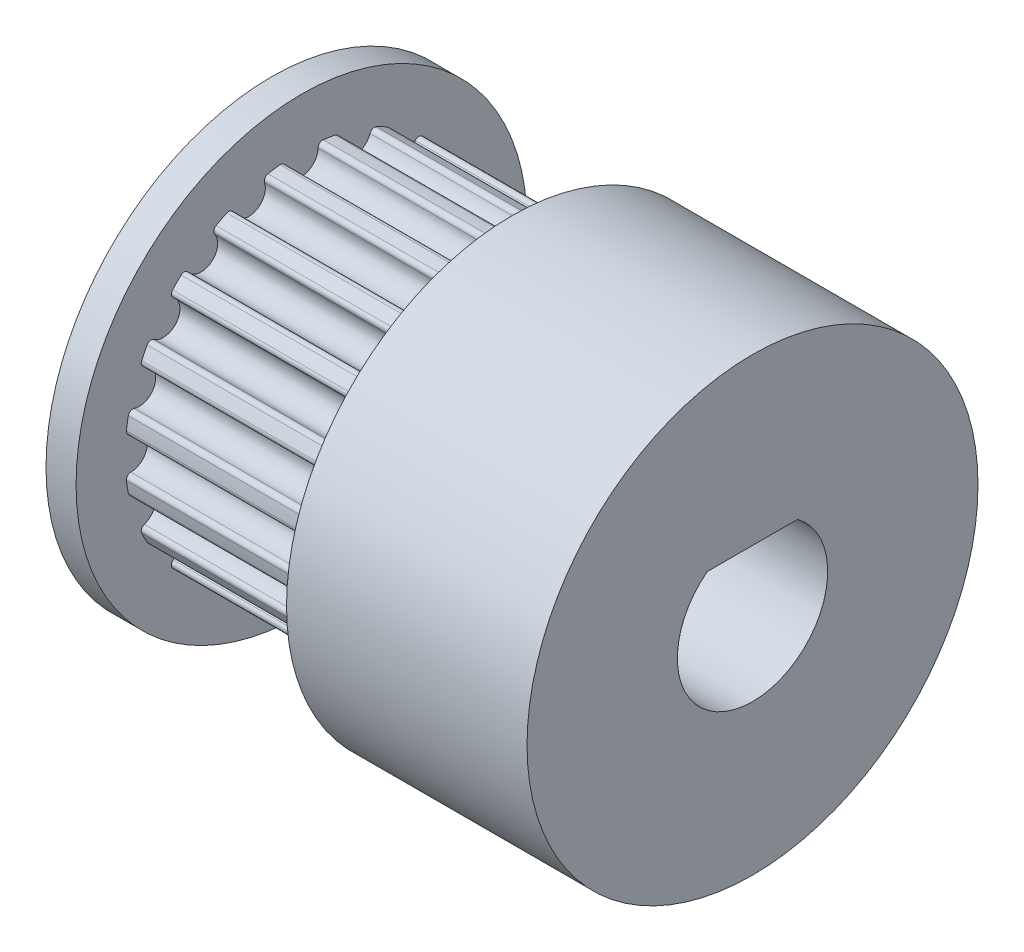
SolidWorks part; units mm, degrees
ref_plane "Front Plane" through (0, 0, 0) normal (0, 0, 1) x (1, 0, 0)
ref_plane "Top Plane" through (0, 0, 0) normal (0, 1, 0) x (1, 0, 0)
ref_plane "Right Plane" through (0, 0, 0) normal (1, 0, 0) x (0, 0, -1)
sketch "Sketch1" plane through (0, 0, 0) normal (0, 0, 1) x (1, 0, 0)
  line L0 (0, 0) -> (-7, 0)
  line L1 (-7, 0) -> (-16, 0)
  line L2 (-16, 0) -> (-16, 7.5)
  line L3 (-16, 7.5) -> (-15, 7.5)
  line L4 (-15, 7.5) -> (-15, 5.87)
  line L5 (-15, 5.87) -> (-8, 5.87)
  line L6 (-8, 5.87) -> (-8, 7.5)
  line L7 (-8, 7.5) -> (-7, 7.5)
  line L8 (-7, 7.5) -> (-7, 0)
  line L9 (0, 0) -> (0, 7.5)
  line L10 (0, 7.5) -> (-7, 7.5)
  dimension "D1" = 7
  dimension "D2" = 9
  dimension "D3" = 7.5
  dimension "D4" = 1
  dimension "D5" = 1.63
  dimension "D6" = 7
  dimension "D7" = 1
  dimension "D8" = 1.63
  dimension "D9" = 7.5
revolve "Revolve1" add sketch "Sketch1" angle 360 about L1
sketch "Sketch2" plane through (-16, 0, 0) normal (-1, 0, 0) x (0, 0, 1)
  line L1 (0, 2) -> (1.5, 2)
  line L2 (0, 2) -> (-1.5, 2)
  arc A0 (-1.5, 2) -> (1.5, 2) centre (0, 0) ccw
  dimension "D1" = 5
  dimension "D2" = 1.5
  dimension "D3" = 1.5
sketch "Sketch3" plane through (-8, 0, 0) normal (-1, 0, 0) x (0, 0, 1)
  arc A0 (0.5242, 5.8465) -> (-0.5242, 5.8465) centre (0, 0) ccw
  arc A1 (-0.5242, 5.8465) -> (0.5242, 5.8465) centre (0, 5.68) ccw
extrude "Cut-Extrude2" cut sketch "Sketch3" along normal blind 7 contours A1 A0
fillet "Fillet1" radius 0.15 2 edges at (-11.5, 5.8465, -0.5242) (-11.5, 5.8465, 0.5242)
pattern_circular "CirPattern1" count 20 over 360 about axis through (0, 0, 0) along (1, 0, 0) of "Cut-Extrude2", "Fillet1"
extrude "Cut-Extrude3" cut sketch "Sketch2" against normal through all both and the other way through all
